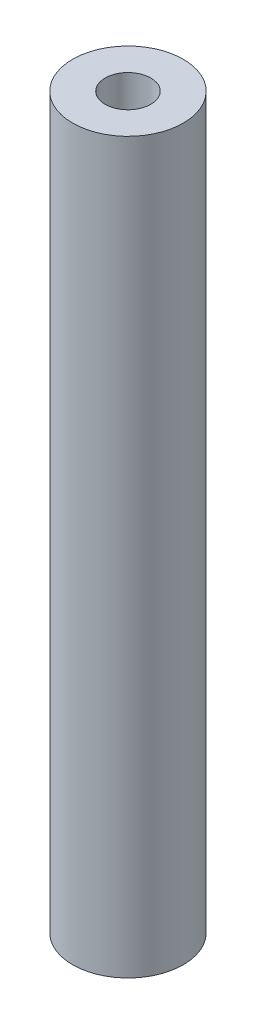
SolidWorks part; units mm, degrees
material "6061-T6 (SS)"
ref_plane "Front Plane" through (0, 0, 0) normal (0, 0, 1) x (1, 0, 0)
ref_plane "Top Plane" through (0, 0, 0) normal (0, 1, 0) x (1, 0, 0)
ref_plane "Right Plane" through (0, 0, 0) normal (1, 0, 0) x (0, 0, -1)
sketch "Sketch1" plane through (0, 0, 0) normal (0, 1, 0) x (1, 0, 0)
  circle A0 centre (0, 0) radius 4
  dimension "D1" = 8
extrude "Boss-Extrude1" add sketch "Sketch1" along normal mid plane 52.7
sketch "Sketch4" plane through (0, 26.35, 0) normal (0, 1, 0) x (1, 0, 0)
  point P0 (0, 0)
hole_wizard "M4x0.7 Tapped Hole1" positions "Sketch4" profile "Sketch3" tap size "M4x0.7" standard "ANSI Metric"
sketch "Sketch3" plane through (0, 26.35, 0) normal (1, 0, 0) x (0, 0, 1)
  line L0 (0, 0) -> (0, 15.9914)
  line L1 (0, 15.9914) -> (1.65, 15)
  line L2 (1.65, 15) -> (1.65, 0)
  line L5 (1.65, 0) -> (0, 0)
  line L10 (0, 15.9914) -> (-1.65, 15) construction
  line L11 (0, -6.35) -> (0, 107.95) construction
  dimension "Tap Drill Dia." = 3.3
  dimension "Tap Drill Depth" = 15
  dimension "Drill Angle" = 118
cosmetic thread "Hole Thread1" parameters "D1"=8, "D2"=4
sketch "Sketch7" plane through (0, -26.35, 0) normal (0, -1, 0) x (-1, 0, 0)
  point P0 (0, 0)
hole_wizard "M4x0.7 Tapped Hole2" positions "Sketch7" profile "Sketch6" tap size "M4x0.7" standard "ANSI Metric"
sketch "Sketch6" plane through (0, -26.35, 0) normal (1, 0, 0) x (0, 0, -1)
  line L0 (0, 0) -> (0, 15.9914)
  line L1 (0, 15.9914) -> (1.65, 15)
  line L2 (1.65, 15) -> (1.65, 0)
  line L5 (1.65, 0) -> (0, 0)
  line L10 (0, 15.9914) -> (-1.65, 15) construction
  line L11 (0, -6.35) -> (0, 107.95) construction
  dimension "Tap Drill Dia." = 3.3
  dimension "Tap Drill Depth" = 15
  dimension "Drill Angle" = 118
cosmetic thread "Hole Thread2" parameters "D1"=8, "D2"=4
